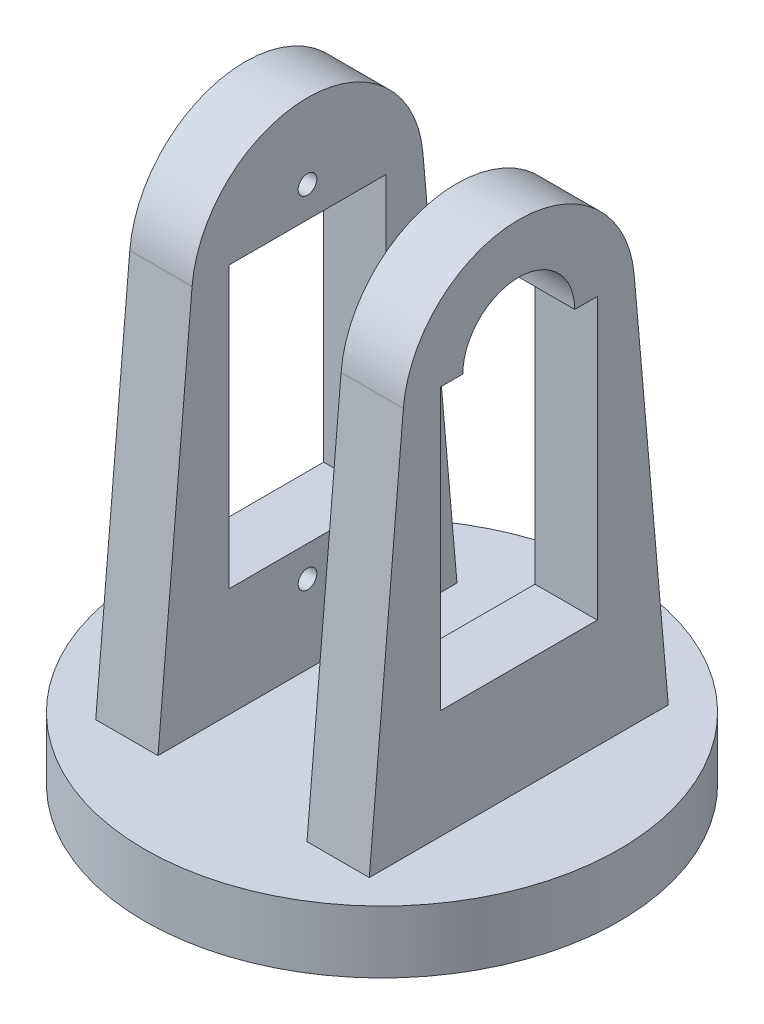
SolidWorks part; units mm, degrees
ref_plane "Front Plane" through (0, 0, 0) normal (0, 0, 1) x (1, 0, 0)
ref_plane "Top Plane" through (0, 0, 0) normal (0, 1, 0) x (1, 0, 0)
ref_plane "Right Plane" through (0, 0, 0) normal (1, 0, 0) x (0, 0, -1)
sketch "Sketch1" plane through (0, 0, 0) normal (0, 1, 0) x (1, 0, 0)
  circle A0 centre (0, 0) radius 2.75
  circle A1 centre (0, 0) radius 19.05
  dimension "D1" = 5.5
  dimension "D2" = 38.1
extrude "Boss-Extrude1" add sketch "Sketch1" along normal blind 5
sketch "Sketch4" plane through (0, 0, 0) normal (0, 1, 0) x (1, 0, 0)
  line L1 (0, 4.6419) -> (-4.02, 2.3209)
  line L2 (-4.02, 2.3209) -> (-4.02, -2.3209)
  line L3 (-4.02, -2.3209) -> (0, -4.6419)
  line L4 (0, -4.6419) -> (4.02, -2.3209)
  line L5 (4.02, -2.3209) -> (4.02, 2.3209)
  line L6 (4.02, 2.3209) -> (0, 4.6419)
  circle A0 centre (0, 0) radius 4.02 construction
  dimension "D1" = 8.04
extrude "Cut-Extrude1" cut sketch "Sketch4" along normal blind 4.1
ref_plane "Plane1" through (-10.98, 0, 0) normal (-1, 0, 0) x (0, 0, 1)
sketch "Sketch5" plane through (-10.98, 0, 0) normal (-1, 0, 0) x (0, 0, 1)
  line L0 (-12, 5) -> (12, 5)
  line L1 (-6.3, 13.75) -> (6.3, 13.75)
  line L2 (-6.3, 13.75) -> (-6.3, 36.25)
  line L3 (-6.3, 36.25) -> (6.3, 36.25)
  line L4 (6.3, 13.75) -> (6.3, 36.25)
  line L5 (-6.3, 13.75) -> (6.3, 36.25) construction
  line L6 (-6.3, 36.25) -> (6.3, 13.75) construction
  line L7 (19.05, 5) -> (-19.05, 5) construction
  line L8 (0, 0) -> (0, -50000) construction
  line L9 (-12, 5) -> (-9.266, 36.25)
  line L10 (12, 5) -> (9.266, 36.25)
  arc A0 (-9.266, 36.25) -> (9.266, 36.25) centre (0, 35.4393) cw
  point P0 (0, 25)
  dimension "D4" = 85
  dimension "D1" = 22.5
  dimension "D2" = 12.6
  dimension "D3" = 25
  dimension "D5" = 12
extrude "Boss-Extrude2" add sketch "Sketch5" against normal blind 5
mirror "Mirror1" about plane through (0, 0, 0) normal (1, 0, 0) of "Boss-Extrude2"
sketch "Sketch6" plane through (-10.98, 0, 0) normal (-1, 0, 0) x (0, 0, 1)
  arc A0 (-0.6692, 40.0585) -> (0.6008, 40.0904) centre (0, 38.716) ccw construction
  arc A1 (0.6008, 9.9096) -> (-0.6692, 9.9415) centre (0, 11.284) ccw construction
  arc A2 (-0.6692, 40.0585) -> (0.6008, 40.0904) centre (0, 38.716) ccw construction
  arc A3 (0.6008, 9.9096) -> (-0.6692, 9.9415) centre (0, 11.284) ccw construction
  arc A4 (-0.6692, 9.9415) -> (0.6008, 9.9096) centre (0, 11.284) ccw construction
  arc A5 (-0.6692, 40.0585) -> (0.6008, 40.0904) centre (0, 38.716) cw construction
  circle A6 centre (0, 38.716) radius 0.75
  circle A7 centre (0, 11.284) radius 0.75
  dimension "D1" = 1.5
extrude "Cut-Extrude2" cut sketch "Sketch6" against normal up to surface (5 mm away) up to face at (-5.98, 25, 0)
sketch "Sketch7" plane through (5.98, 0, 0) normal (-1, 0, 0) x (0, 0, 1)
  line L0 (6.3, 36.25) -> (-6.3, 36.25) construction
  line L1 (-4.4907, 36.25) -> (4.4907, 36.25)
  arc A0 (4.4907, 36.25) -> (-4.4907, 36.25) centre (0, 36.25) ccw
  arc A4 (9.266, 36.25) -> (-9.266, 36.25) centre (0, 35.4393) ccw construction
  arc A5 (9.266, 36.25) -> (-9.266, 36.25) centre (0, 35.4393) ccw construction
  circle A6 centre (0, 36.25) radius 8.4907 construction
  dimension "D1" = 4
extrude "Cut-Extrude3" cut sketch "Sketch7" against normal up to surface (5 mm away) up to face at (10.98, 22.7477, 0)
